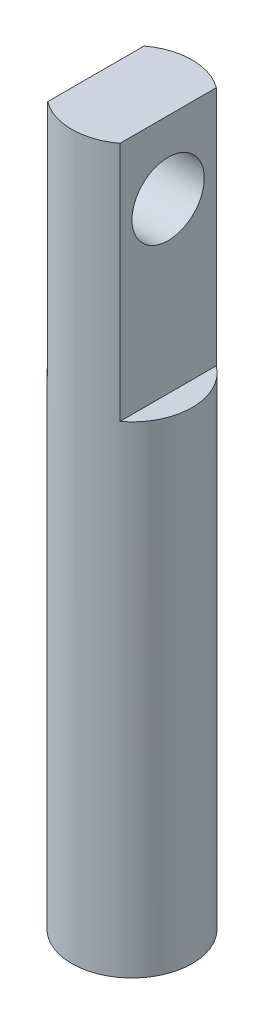
SolidWorks part; units mm, degrees
ref_plane "정면" through (0, 0, 0) normal (0, 0, 1) x (1, 0, 0)
ref_plane "윗면" through (0, 0, 0) normal (0, 1, 0) x (1, 0, 0)
ref_plane "우측면" through (0, 0, 0) normal (1, 0, 0) x (0, 0, -1)
sketch "Sketch1" plane through (0, 0, 0) normal (0, 1, 0) x (1, 0, 0)
  circle A0 centre (0, 0) radius 2.54
  dimension "D1" = 5.08
extrude "Extrude1" add sketch "Sketch1" along normal blind 30.48
sketch "Sketch2" plane through (0, 30.48, 0) normal (0, 1, 0) x (-1, 0, 0)
  line L1 (-1.524, -4.7981) -> (-3.556, -4.7981)
  line L2 (-1.524, -4.7981) -> (-1.524, 5.1537)
  line L3 (-1.524, 5.1537) -> (-3.556, 5.1537)
  line L4 (-3.556, -4.7981) -> (-3.556, 5.1537)
  line L5 (3.4733, -3.953) -> (1.524, -3.953)
  line L6 (3.4733, -3.953) -> (3.4733, 5.1537)
  line L7 (3.4733, 5.1537) -> (1.524, 5.1537)
  line L8 (1.524, -3.953) -> (1.524, 5.1537)
  circle A0 centre (0, 0) radius 2.54 construction
  dimension "D1" = 3.048
  dimension "D2" = 1.524
  dimension "D3" = 2.032
extrude "Cut-Extrude1" cut sketch "Sketch2" against normal blind 10.16
sketch "Sketch4" plane through (-1.524, 0, 0) normal (-1, 0, 0) x (0, 0, 1)
  line L0 (2.032, 30.48) -> (-2.032, 30.48) construction
  line L1 (-2.032, 20.32) -> (-2.032, 30.48) construction
  circle A0 centre (0, 27.432) radius 1.524
  point P2 (0, 30.48)
  dimension "D3" = 3.048
  dimension "D1" = 3.048
  dimension "D2" = 2.032
extrude "Cut-Extrude2" cut sketch "Sketch4" against normal blind 10
